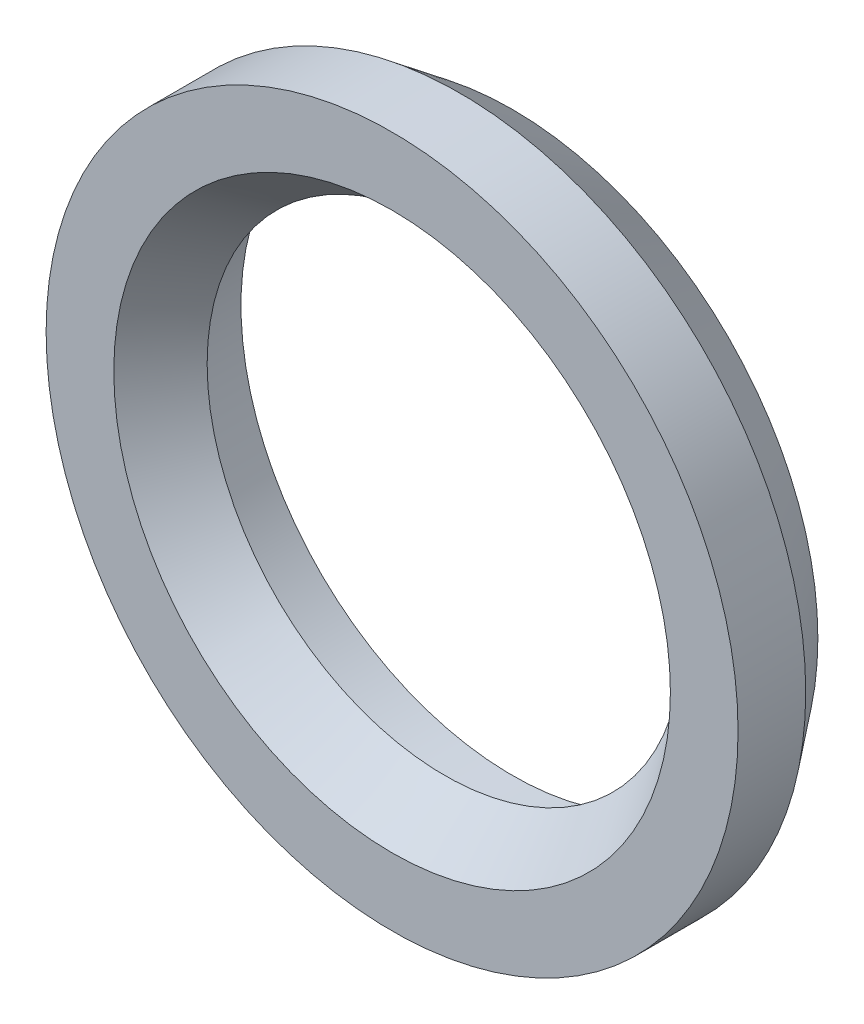
SolidWorks part; units mm, degrees
ref_plane "Front Plane" through (0, 0, 0) normal (0, 0, 1) x (1, 0, 0)
ref_plane "Top Plane" through (0, 0, 0) normal (0, 1, 0) x (1, 0, 0)
ref_plane "Right Plane" through (0, 0, 0) normal (1, 0, 0) x (0, 0, -1)
sketch "Sketch3" plane through (0, 0, 0) normal (0, 1, 0) x (1, 0, 0)
  line L0 (0, 0) -> (0, 21.5051) construction
  line L1 (0, 0) -> (40.125, 0) construction
  line L2 (40.125, 0) -> (40.125, 10)
  line L3 (40.125, 10) -> (45.125, 10)
  line L4 (45.125, 10) -> (51.125, 2.2051)
  line L5 (51.125, 2.2051) -> (51.125, -7.7949)
  line L9 (35.125, 0) -> (40.125, 0)
  line L10 (51.125, -7.7949) -> (41.125, -7.7949)
  line L11 (35.125, 0) -> (41.125, -7.7949)
  dimension "D1" = 40.125
  dimension "D2" = 10
  dimension "D3" = 5
  dimension "D4" = 10
  dimension "D5" = 6
  dimension "D6" = 10
revolve "Revolve1" add sketch "Sketch3" angle 360 about L0
